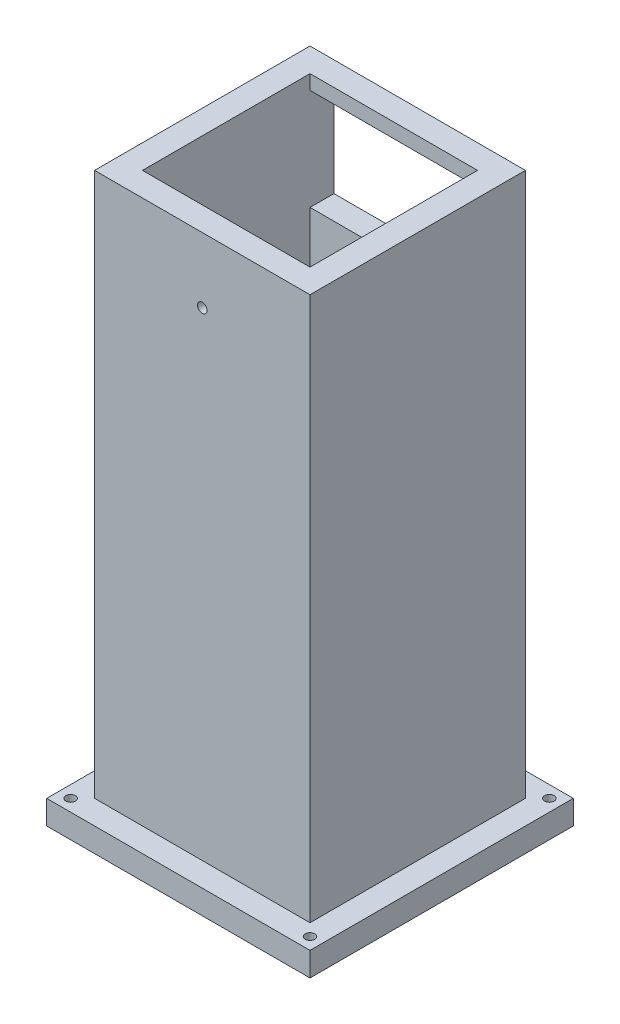
SolidWorks part; units mm, degrees
ref_plane "Alzado" through (0, 0, 0) normal (0, 0, 1) x (1, 0, 0)
ref_plane "Planta" through (0, 0, 0) normal (0, 1, 0) x (1, 0, 0)
ref_plane "Vista lateral" through (0, 0, 0) normal (1, 0, 0) x (0, 0, -1)
sketch "Croquis1" plane through (0, 0, 0) normal (0, 1, 0) x (1, 0, 0)
  line L1 (-22.5, -22.5) -> (22.5, -22.5)
  line L2 (-22.5, -22.5) -> (-22.5, 22.5)
  line L3 (-22.5, 22.5) -> (22.5, 22.5)
  line L4 (22.5, -22.5) -> (22.5, 22.5)
  line L5 (-22.5, -22.5) -> (22.5, 22.5) construction
  line L6 (-22.5, 22.5) -> (22.5, -22.5) construction
  point P0 (0, 0)
  dimension "D1" = 45
  dimension "D2" = 45
extrude "Saliente-Extruir1" add sketch "Croquis1" along normal blind 300
sketch "Croquis4" plane through (-22.5, 0, 0) normal (-1, 0, 0) x (0, 0, 1)
  line L1 (22.5, 300) -> (22.5, 0) construction
  line L3 (55, 0) -> (-55, 0) construction
  line L5 (4.5, 0) -> (4.5, 34)
  line L6 (4.5, 34) -> (22.5, 34)
  line L8 (22.5, 34) -> (22.5, 0)
  line L9 (22.5, 0) -> (4.5, 0)
  dimension "D4" = 34
extrude "Cortar-Extruir2" cut sketch "Croquis4" against normal through all
sketch "Croquis7" plane through (0, 0, 22.5) normal (0, 0, 1) x (1, 0, 0)
  line L0 (0, -24.75) -> (0, 24.75) construction
  line L1 (-22.5, 246.3879) -> (22.5, 246.3879)
  line L2 (-22.5, 246.3879) -> (-22.5, 273.6121)
  line L3 (-22.5, 273.6121) -> (22.5, 273.6121)
  line L4 (22.5, 246.3879) -> (22.5, 273.6121)
  line L5 (-22.5, 246.3879) -> (22.5, 273.6121) construction
  line L6 (-22.5, 273.6121) -> (22.5, 246.3879) construction
  line L7 (22.5, 300) -> (22.5, 34) construction
  point P0 (0, 260)
  dimension "D1" = 260
sketch "Croquis8" plane through (0, 300, 0) normal (0, 1, 0) x (1, 0, 0)
  line L0 (22.5, -22.5) -> (22.5, 22.5) construction
  line L1 (-17.5, -17.5) -> (17.5, -17.5)
  line L2 (-17.5, -17.5) -> (-17.5, 17.5)
  line L3 (-17.5, 17.5) -> (17.5, 17.5)
  line L4 (17.5, -17.5) -> (17.5, 17.5)
  line L5 (-17.5, -17.5) -> (17.5, 17.5) construction
  line L6 (-17.5, 17.5) -> (17.5, -17.5) construction
  line L7 (22.5, 22.5) -> (-22.5, 22.5) construction
  point P0 (0, 0)
  dimension "D1" = 5
  dimension "D2" = 5
extrude "Cortar-Extruir3" cut sketch "Croquis8" against normal through all contours L3 L4 L1 L2
sketch "Croquis9" plane through (0, 0, -22.5) normal (0, 0, -1) x (-1, 0, 0)
  line L0 (22.5, 273.6121) -> (-22.5, 246.3879) construction
  line L1 (-17.5, 249.4128) -> (17.5, 249.4128)
  line L2 (-17.5, 249.4128) -> (-17.5, 270.5872)
  line L3 (-17.5, 270.5872) -> (17.5, 270.5872)
  line L4 (17.5, 249.4128) -> (17.5, 270.5872)
  line L5 (-17.5, 249.4128) -> (17.5, 270.5872) construction
  line L6 (-17.5, 270.5872) -> (17.5, 249.4128) construction
  line L7 (22.5, 246.3879) -> (22.5, 273.6121) construction
  point P0 (0, 260)
  point P10 (22.5, 260)
  dimension "D1" = 5
extrude "Cortar-Extruir4" cut sketch "Croquis9" against normal blind 10 contours L4 L3 L2 L1
sketch "Croquis10" plane through (0, 0, 22.5) normal (0, 0, 1) x (1, 0, 0)
  circle A0 centre (0, 260) radius 1
  dimension "D1" = 2
extrude "Cortar-Extruir5" cut sketch "Croquis10" against normal blind 10
sketch "Croquis11" plane through (0, 0, 22.5) normal (0, 0, 1) x (1, 0, 0)
  line L0 (22.5, 300) -> (22.5, 34) construction
  line L1 (-22.5, 300) -> (22.5, 300)
  line L2 (-22.5, 300) -> (-22.5, 273.6121)
  line L3 (-22.5, 273.6121) -> (22.5, 273.6121)
  line L4 (22.5, 300) -> (22.5, 273.6121)
  line L5 (-22.5, 273.6121) -> (22.5, 273.6121) construction
  dimension "D1" = 0
extrude "Cortar-Extruir6" cut sketch "Croquis11" against normal through all
sketch "Croquis12" plane through (0, 0, 22.5) normal (0, 0, 1) x (1, 0, 0)
  line L0 (-22.5, 267.3717) -> (22.5, 246.3879)
  line L1 (-22.5, 246.3879) -> (-22.5, 273.6121) construction
  line L2 (-22.5, 246.3879) -> (22.5, 246.3879) construction
  dimension "D1" = 25
sketch "Croquis13" plane through (0, 0, 0) normal (1, 0, 0) x (0, 0, -1)
  line L0 (-22.5, 273.6121) -> (-22.5, 34) construction
  line L1 (-22.5, 160) -> (22.5, 160)
  line L2 (-22.5, 160) -> (-22.5, 0)
  line L3 (-22.5, 0) -> (22.5, 0)
  line L4 (22.5, 160) -> (22.5, 0)
  line L5 (24.75, 0) -> (-24.75, 0) construction
  line L6 (22.5, 273.6121) -> (22.5, 0) construction
  dimension "D1" = 160
extrude "Cortar-Extruir7" cut sketch "Croquis13" against normal through all both and the other way through all
sketch "Croquis14" plane through (0, 160, 0) normal (0, -1, 0) x (1, 0, 0)
  line L1 (-27.5, -27.5) -> (27.5, -27.5)
  line L2 (-27.5, -27.5) -> (-27.5, 27.5)
  line L3 (-27.5, 27.5) -> (27.5, 27.5)
  line L4 (27.5, -27.5) -> (27.5, 27.5)
  line L5 (-27.5, -27.5) -> (27.5, 27.5) construction
  line L6 (-27.5, 27.5) -> (27.5, -27.5) construction
  point P0 (0, 0)
  dimension "D1" = 27.5
  dimension "D2" = 27.5
extrude "Saliente-Extruir2" add sketch "Croquis14" along normal blind 5 contours L3 L4 L1 L2
sketch "Croquis16" plane through (0, 155, 0) normal (0, -1, 0) x (1, 0, 0)
  circle A0 centre (25, 25) radius 1
  circle A1 centre (-25, 25) radius 1
  circle A2 centre (-25, -25) radius 1
  circle A3 centre (25, -25) radius 1
  dimension "D1" = 2
  dimension "D2" = 2.5
  dimension "D3" = 2.5
  dimension "D4" = 2.5
  dimension "D5" = 2.5
extrude "Cortar-Extruir8" cut sketch "Croquis16" against normal through all both
